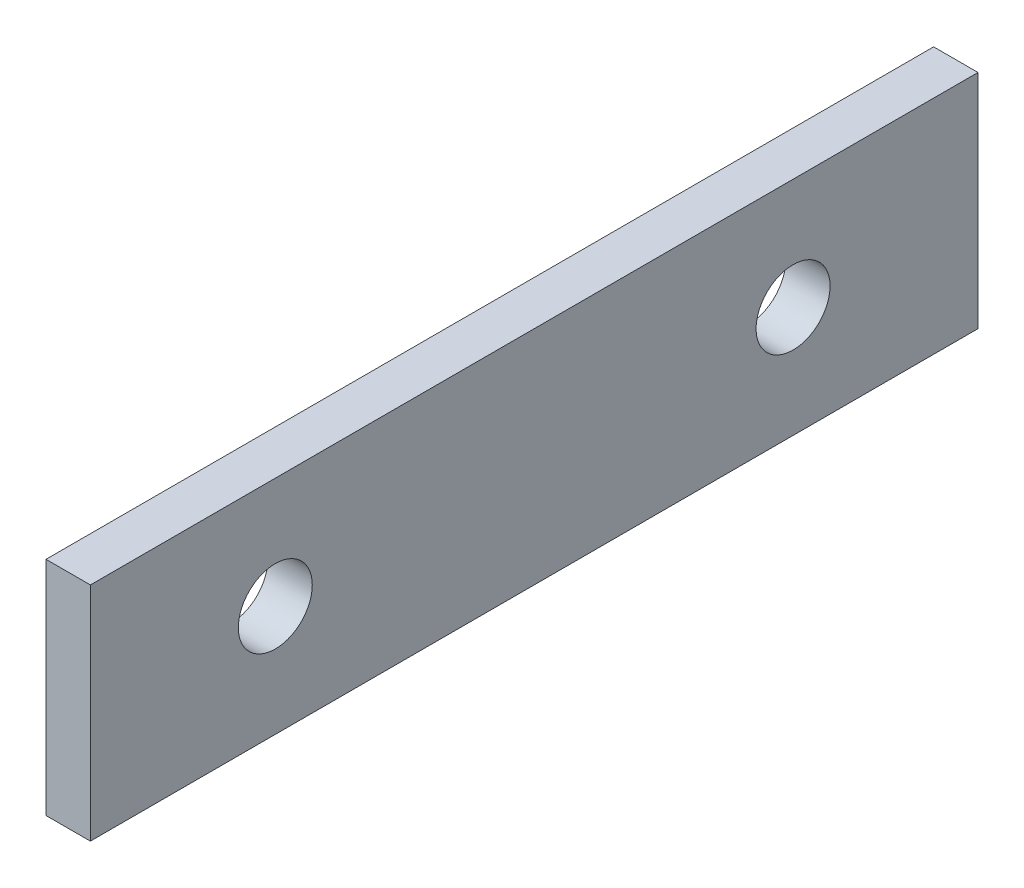
SolidWorks part; units mm, degrees
ref_plane "Front Plane" through (0, 0, 0) normal (0, 0, 1) x (1, 0, 0)
ref_plane "Top Plane" through (0, 0, 0) normal (0, 1, 0) x (1, 0, 0)
ref_plane "Right Plane" through (0, 0, 0) normal (1, 0, 0) x (0, 0, -1)
sketch "Sketch1" plane through (0, 0, 0) normal (1, 0, 0) x (0, 0, -1)
  line L0 (-17.5, -7.5) -> (17.5, -7.5) construction
  line L1 (-30, 0) -> (30, 0)
  line L2 (-30, 0) -> (-30, -15)
  line L3 (-30, -15) -> (30, -15)
  line L4 (30, 0) -> (30, -15)
  circle A0 centre (-17.5, -7.5) radius 2.5
  circle A1 centre (17.5, -7.5) radius 2.5
  point P4 (0, 0)
  point P12 (-30, -7.5)
  point P16 (0, -7.5)
  dimension "D3" = 5
  dimension "D1" = 60
  dimension "D2" = 15
  dimension "D4" = 35
extrude "Boss-Extrude1" add sketch "Sketch1" along normal blind 3
